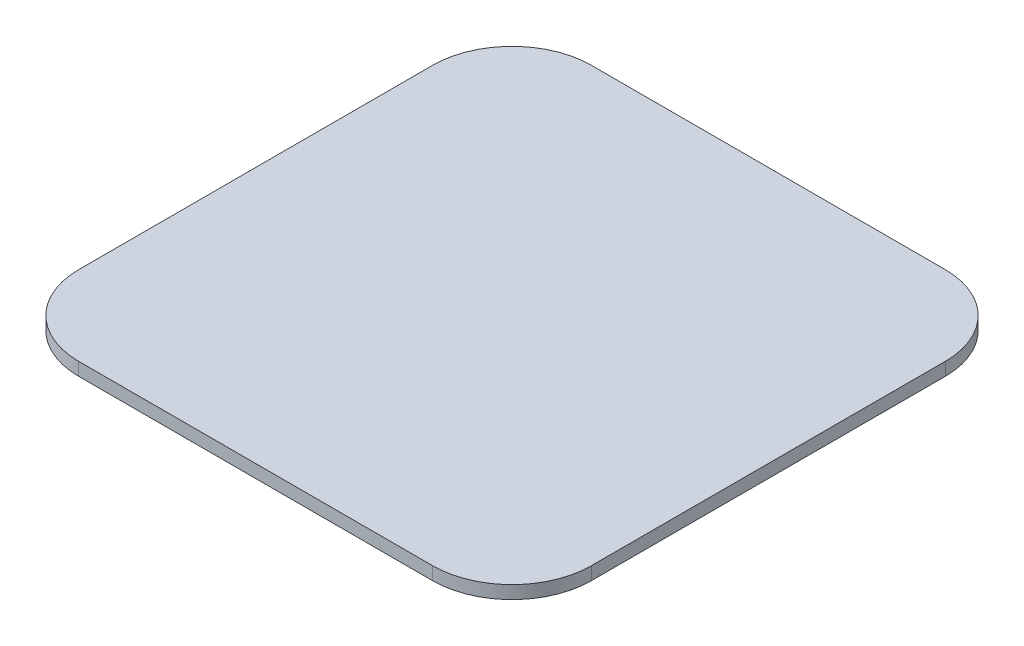
SolidWorks part; units mm, degrees
material "Acrylic (Medium-high impact)"
ref_plane "Front Plane" through (0, 0, 0) normal (0, 0, 1) x (1, 0, 0)
ref_plane "Top Plane" through (0, 0, 0) normal (0, 1, 0) x (1, 0, 0)
ref_plane "Right Plane" through (0, 0, 0) normal (1, 0, 0) x (0, 0, -1)
sketch "Sketch1" plane through (0, 0, 0) normal (0, 1, 0) x (1, 0, 0)
  line L1 (24.5, -35.5) -> (-24.5, -35.5)
  line L2 (35.5, -24.5) -> (35.5, 24.5)
  line L3 (24.5, 35.5) -> (-24.5, 35.5)
  line L4 (-35.5, -24.5) -> (-35.5, 24.5)
  line L5 (35.5, -35.5) -> (-35.5, 35.5) construction
  line L6 (35.5, 35.5) -> (-35.5, -35.5) construction
  arc A0 (-24.5, -35.5) -> (-35.5, -24.5) centre (-24.5, -24.5) cw
  arc A1 (24.5, -35.5) -> (35.5, -24.5) centre (24.5, -24.5) ccw
  arc A2 (35.5, 24.5) -> (24.5, 35.5) centre (24.5, 24.5) ccw
  arc A3 (-24.5, 35.5) -> (-35.5, 24.5) centre (-24.5, 24.5) ccw
  point P0 (0, 0)
  dimension "D3" = 11
  dimension "D1" = 35.5
  dimension "D2" = 35.5
extrude "Boss-Extrude1" add sketch "Sketch1" along normal blind 1.8
